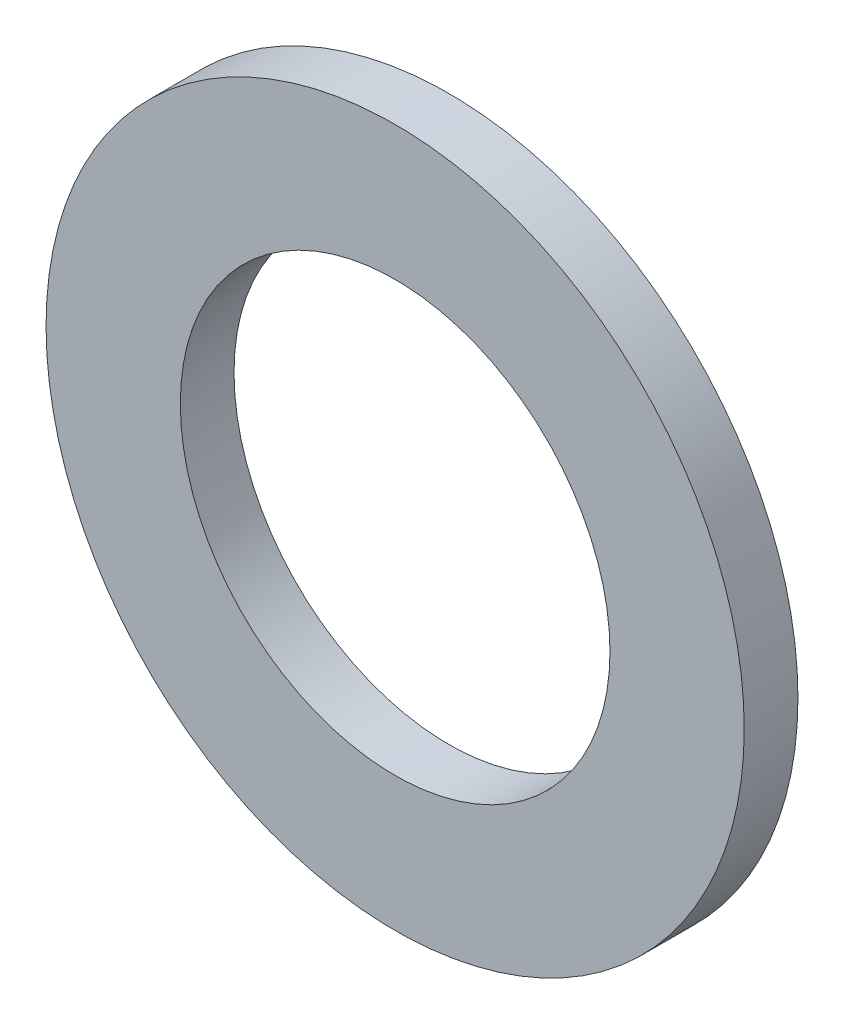
SolidWorks part; units mm, degrees
ref_plane "Front Plane" through (0, 0, 0) normal (0, 0, 1) x (1, 0, 0)
ref_plane "Top Plane" through (0, 0, 0) normal (0, 1, 0) x (1, 0, 0)
ref_plane "Right Plane" through (0, 0, 0) normal (1, 0, 0) x (0, 0, -1)
sketch "Sketch1" plane through (0, 0, 0) normal (0, 0, 1) x (1, 0, 0)
  circle A0 centre (0, 0) radius 4
  circle A1 centre (0, 0) radius 6.5
  dimension "D1" = 8
  dimension "D2" = 13
extrude "Boss-Extrude1" add sketch "Sketch1" along normal blind 1
